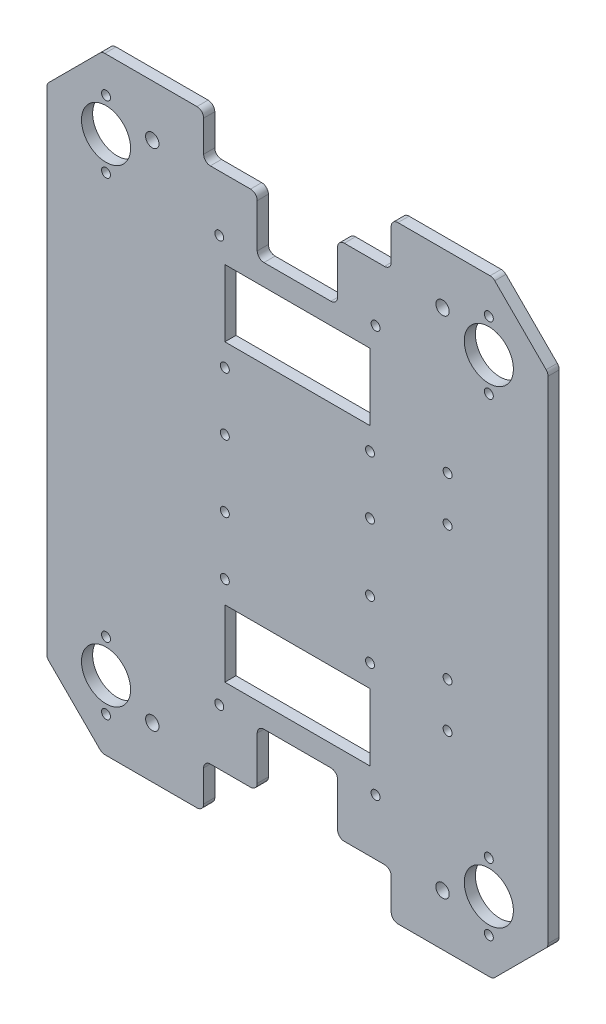
SolidWorks part; units mm, degrees
material "Alliage 1060"
ref_plane "Plan de dessus" through (0, 0, 0) normal (0, 0, 1) x (1, 0, 0)
ref_plane "Plan de droite" through (0, 0, 0) normal (0, 1, 0) x (1, 0, 0)
ref_plane "Plan de face" through (0, 0, 0) normal (1, 0, 0) x (0, 0, -1)
sketch "Esquisse1" plane through (0, 0, 0) normal (0, 0, 1) x (1, 0, 0)
  line L0 (0, 0) -> (-175, 0)
  line L1 (-175, 0) -> (-199.7487, 24.7487)
  line L2 (-199.7487, 24.7487) -> (-199.7487, 247.2487)
  line L3 (-199.7487, 247.2487) -> (-175, 271.9975)
  line L4 (-175, 271.9975) -> (0, 271.9975)
  line L5 (0, 271.9975) -> (24.7487, 247.2487)
  line L6 (24.7487, 247.2487) -> (24.7487, 24.7487)
  line L7 (24.7487, 24.7487) -> (0, 0)
  dimension "D1" = 222.5
  dimension "D2" = 35
  dimension "D3" = 135
  dimension "D4" = 175
extrude "Base" add sketch "Esquisse1" along normal blind 5
sketch "Esquisse3" plane through (0, 0, 0) normal (0, 0, -1) x (-1, 0, 0)
  line L0 (129.5, 0) -> (129.5, 20)
  line L1 (175, 0) -> (0, 0) construction
  line L2 (129.5, 20) -> (105.5, 20)
  line L3 (105.5, 20) -> (105.5, 45.5)
  line L4 (105.5, 45.5) -> (69.5, 45.5)
  line L5 (69.5, 45.5) -> (69.5, 20)
  line L6 (69.5, 20) -> (45.5, 20)
  line L7 (45.5, 20) -> (45.5, 0)
  line L8 (-24.7487, 135.9987) -> (199.7487, 135.9987) construction
  line L9 (-24.7487, 24.7487) -> (-24.7487, 247.2487) construction
  line L10 (199.7487, 247.2487) -> (199.7487, 24.7487) construction
  line L11 (45.5, 0) -> (129.5, 0)
  line L12 (45.5, 271.9975) -> (129.5, 271.9975)
  line L13 (129.5, 271.9975) -> (129.5, 251.9975)
  line L14 (129.5, 251.9975) -> (105.5, 251.9975)
  line L15 (105.5, 251.9975) -> (105.5, 226.4975)
  line L16 (105.5, 226.4975) -> (69.5, 226.4975)
  line L17 (69.5, 226.4975) -> (69.5, 251.9975)
  line L18 (69.5, 251.9975) -> (45.5, 251.9975)
  line L19 (45.5, 251.9975) -> (45.5, 271.9975)
  line L20 (87.5, 45.5) -> (87.5, -49954.5) construction
  line L21 (0, 271.9975) -> (175, 271.9975) construction
  line L22 (55, 216.9975) -> (120, 216.9975)
  line L23 (55, 216.9975) -> (55, 186.9975)
  line L24 (55, 186.9975) -> (120, 186.9975)
  line L25 (120, 216.9975) -> (120, 186.9975)
  line L26 (120, 55) -> (120, 85)
  line L27 (55, 85) -> (120, 85)
  line L28 (55, 55) -> (120, 55)
  line L29 (55, 55) -> (55, 85)
  circle A0 centre (52.5, 45) radius 2
  circle A1 centre (122.5, 45) radius 2
  circle A2 centre (122.5, 226.9975) radius 2
  circle A3 centre (52.5, 226.9975) radius 2
  point P4 (87.5, 45.5)
  point P11 (87.5, 0)
  point P40 (87.5, 216.9975)
  dimension "D7" = 4
  dimension "D5" = 25
  dimension "D1" = 20
  dimension "D2" = 24
  dimension "D3" = 36
  dimension "D4" = 25.5
  dimension "D6" = 7
  dimension "D8" = 55
  dimension "D9" = 30
  dimension "D10" = 65
extrude "Enlèv. mat.-Extru.1" cut sketch "Esquisse3" against normal through all
fillet "Congé1" radius 3 24 edges at (-199.7487, 24.7487, 2.5) (24.7487, 24.7487, 2.5) (0, 0, 2.5) (-129.5, 20, 2.5) (-105.5, 45.5, 2.5) (-105.5, 20, 2.5) (-175, 0, 2.5) (-129.5, 0, 2.5) (-69.5, 45.5, 2.5) (-45.5, 20, 2.5) (-69.5, 20, 2.5) (-45.5, 0, 2.5) (24.7487, 247.2487, 2.5) (-129.5, 251.9975, 2.5) (-105.5, 226.4975, 2.5) (-199.7487, 247.2487, 2.5) (-175, 271.9975, 2.5) (-129.5, 271.9975, 2.5) (-105.5, 251.9975, 2.5) (-69.5, 226.4975, 2.5) (-45.5, 251.9975, 2.5) (-69.5, 251.9975, 2.5) (-45.5, 271.9975, 2.5) (0, 271.9975, 2.5)
sketch "Esquisse6" plane through (0, 0, 5) normal (0, 0, 1) x (1, 0, 0)
  line L0 (-173.2157, 225.9975) -> (-173.2157, 240.9975) construction
  line L2 (-87.5, 231.5685) -> (-87.5, -49768.4315) construction
  line L4 (-55, 186.9975) -> (-120, 186.9975) construction
  line L5 (-203.2843, 135.9987) -> (49796.7157, 135.9987) construction
  line L6 (-199.7487, 246.0061) -> (-199.7487, 25.9914) construction
  line L7 (-1.7843, 255.9975) -> (-1.7843, 225.9975) construction
  line L8 (-1.7843, 46) -> (-1.7843, 16) construction
  line L9 (-42.5, 0) -> (-1.2426, 0) construction
  line L11 (-173.2157, 46) -> (-173.2157, 31) construction
  line L13 (-173.2157, 31) -> (-173.2157, 16) construction
  line L15 (-173.7574, 0) -> (-132.5, 0) construction
  line L18 (-132.5, 271.9975) -> (-173.7574, 271.9975) construction
  circle A2 centre (-1.7843, 16) radius 2
  circle A3 centre (-1.7843, 46) radius 2
  circle A4 centre (-1.7843, 225.9975) radius 2
  circle A5 centre (-1.7843, 255.9975) radius 2
  circle A10 centre (-1.7843, 240.9975) radius 11
  circle A11 centre (-1.7843, 31) radius 11
  circle A25 centre (-173.2157, 16) radius 2
  circle A26 centre (-173.2157, 46) radius 2
  circle A27 centre (-173.2157, 31) radius 11
  circle A28 centre (-173.2157, 225.9975) radius 2
  circle A29 centre (-173.2157, 255.9975) radius 2
  circle A30 centre (-173.2157, 240.9975) radius 11
  point P15 (-87.5, 186.9975)
  point P20 (-199.7487, 135.9987)
  dimension "D2" = 15
  dimension "D3" = 22
  dimension "D4" = 30
  dimension "D5" = 31
  dimension "D7" = 31
  dimension "D8" = 22
  dimension "D10" = 30
  dimension "D6" = 22
  dimension "D13" = 22
  dimension "D14" = 30
  dimension "D15" = 31
extrude "Perçage pour billes" cut sketch "Esquisse6" against normal up to next
sketch "Esquisse8" plane through (0, 0, 5) normal (0, 0, 1) x (1, 0, 0)
  line L0 (-87.5, 226.4975) -> (-87.5, 85) construction
  line L1 (-72.5, 226.4975) -> (-102.5, 226.4975) construction
  line L2 (-120, 85) -> (-55, 85) construction
  line L3 (-132.5, 271.9975) -> (-173.7574, 271.9975) construction
  line L4 (-129.5, 254.9975) -> (-129.5, 268.9975) construction
  line L5 (-173.7574, 0) -> (-132.5, 0) construction
  line L6 (-129.5, 3) -> (-129.5, 17) construction
  circle A0 centre (-152.5, 23) radius 3
  circle A1 centre (-152.5, 248.9975) radius 3
  circle A2 centre (-22.5, 248.9975) radius 3
  circle A3 centre (-22.5, 23) radius 3
  dimension "D1" = 23
  dimension "D2" = 23
  dimension "D3" = 6
  dimension "D4" = 23
  dimension "D5" = 23
  dimension "D6" = 6
extrude "Perçage pour profilé" cut sketch "Esquisse8" against normal up to next
sketch "Esquisse13" plane through (0, 0, 5) normal (0, 0, 1) x (1, 0, 0)
  line L0 (24.7487, 135.9987) -> (-199.7487, 135.9987) construction
  line L1 (24.7487, 25.9914) -> (24.7487, 246.0061) construction
  line L2 (-199.7487, 246.0061) -> (-199.7487, 25.9914) construction
  circle A0 centre (-20.2513, 185.9987) radius 2
  circle A1 centre (-20.2513, 165.9987) radius 2
  circle A2 centre (-20.2513, 105.9987) radius 2
  circle A3 centre (-20.2513, 85.9987) radius 2
  dimension "D1" = 4
  dimension "D2" = 4
  dimension "D3" = 20
  dimension "D4" = 30
  dimension "D5" = 45
extrude "Enlèv. mat.-Extru.4" cut sketch "Esquisse13" against normal blind 10
sketch "Esquisse14" plane through (0, 0, 5) normal (0, 0, 1) x (1, 0, 0)
  line L0 (-55, 186.9975) -> (-120, 186.9975) construction
  line L1 (-120, 186.9975) -> (-120, 216.9975) construction
  line L2 (-55, 216.9975) -> (-55, 186.9975) construction
  line L3 (-199.7487, 135.9987) -> (24.7487, 135.9987) construction
  line L4 (-199.7487, 246.0061) -> (-199.7487, 25.9914) construction
  line L5 (24.7487, 25.9914) -> (24.7487, 246.0061) construction
  circle A0 centre (-120, 176.9975) radius 2
  circle A1 centre (-55, 176.9975) radius 2
  circle A2 centre (-120, 150.9975) radius 2
  circle A3 centre (-55, 150.9975) radius 2
  circle A4 centre (-120, 121) radius 2
  circle A5 centre (-55, 121) radius 2
  circle A6 centre (-55, 95) radius 2
  circle A7 centre (-120, 95) radius 2
  dimension "D1" = 10
  dimension "D2" = 10
  dimension "D3" = 36
  dimension "D4" = 36
  dimension "D5" = 0
  dimension "D6" = 0
  dimension "D7" = 0
  dimension "D8" = 0
extrude "Enlèv. mat.-Extru.5" cut sketch "Esquisse14" against normal blind 10
